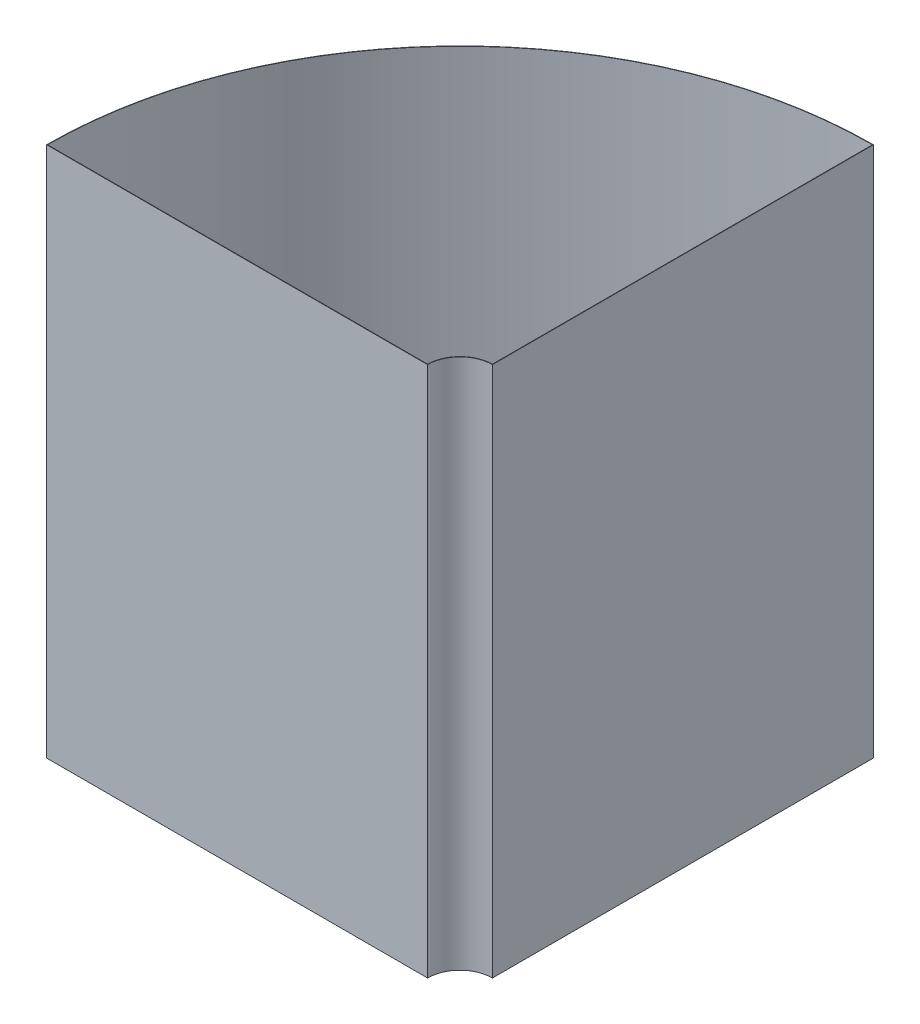
SolidWorks part; units mm, degrees
ref_plane "Front Plane" through (0, 0, 0) normal (0, 0, 1) x (1, 0, 0)
ref_plane "Top Plane" through (0, 0, 0) normal (0, 1, 0) x (1, 0, 0)
ref_plane "Right Plane" through (0, 0, 0) normal (1, 0, 0) x (0, 0, -1)
sketch "Sketch1" plane through (0, 0, 0) normal (0, 1, 0) x (1, 0, 0)
  line L0 (0, 350.175) -> (0, 27.5) construction
  line L1 (-350.175, 0) -> (-27.5, 0) construction
  line L2 (-350.175, 0) -> (-27.5, 0)
  line L3 (0, 0) -> (0, 0.35)
  line L5 (0, 0) -> (0, 0.35)
  line L7 (0, 27.5) -> (0, 350.175)
  line L8 (0, 0.35) -> (0, 0) construction
  line L9 (0, 27.5) -> (0, 0) construction
  line L10 (-27.5, 0) -> (0, 0) construction
  arc A0 (0, 350.175) -> (-350.175, 0) centre (0, 0) ccw
  arc A2 (0, 27.5) -> (-27.5, 0) centre (0, 0) ccw
  dimension "D1" = 700.35
  dimension "D2" = 55
extrude "Boss-Extrude1" add sketch "Sketch1" along normal blind 450
shell "Shell1" thickness 0.35
